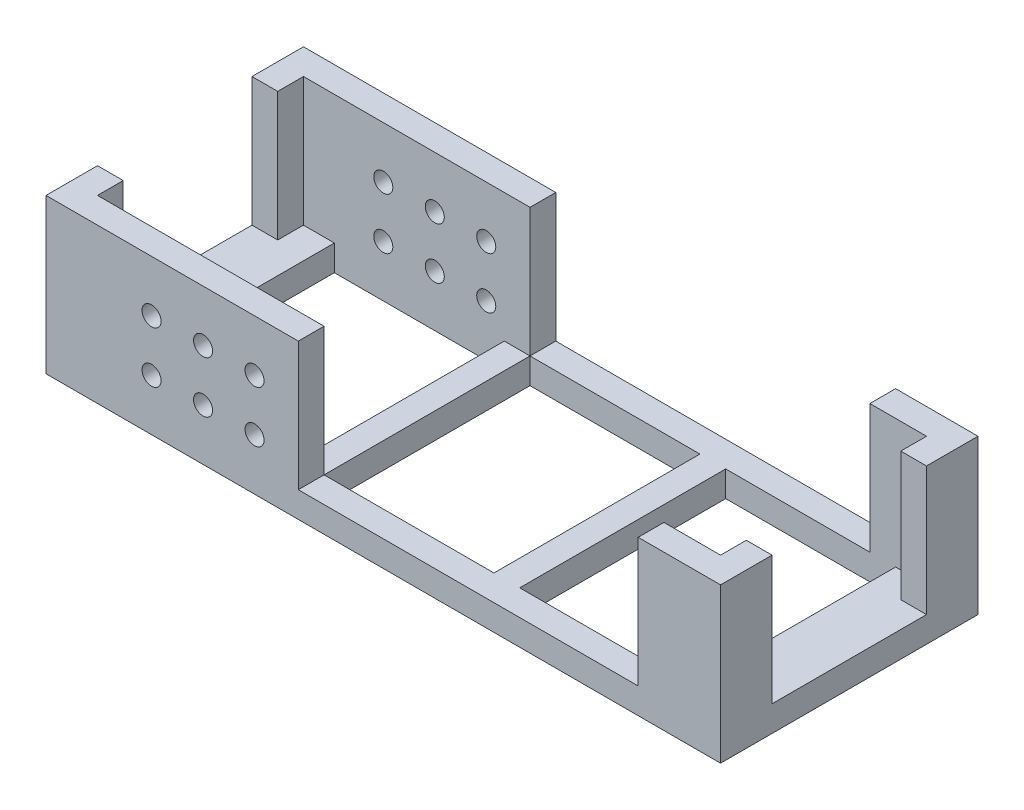
SolidWorks part; units mm, degrees
ref_plane "Front Plane" through (0, 0, 0) normal (0, 0, 1) x (1, 0, 0)
ref_plane "Top Plane" through (0, 0, 0) normal (0, 1, 0) x (1, 0, 0)
ref_plane "Right Plane" through (0, 0, 0) normal (1, 0, 0) x (0, 0, -1)
sketch "Sketch1" plane through (0, 0, 0) normal (0, 1, 0) x (1, 0, 0)
  line L1 (-65.5, -25) -> (65.5, -25)
  line L2 (-65.5, -25) -> (-65.5, 25)
  line L3 (-65.5, 25) -> (65.5, 25)
  line L4 (65.5, -25) -> (65.5, 25)
  line L5 (-65.5, -25) -> (65.5, 25) construction
  line L6 (-65.5, 25) -> (65.5, -25) construction
  point P0 (0, 0)
extrude "Boss-Extrude6" add sketch "Sketch1" along normal blind 5
sketch "Sketch11" plane through (0, 0, 0) normal (0, 1, 0) x (1, 0, 0)
  line L0 (54.5, -20) -> (21.5, -20)
  line L1 (16.5, -20) -> (-16.5, -20)
  line L2 (16.5, -20) -> (16.5, 20)
  line L3 (16.5, 20) -> (-16.5, 20)
  line L4 (-16.5, -20) -> (-16.5, 20)
  line L5 (16.5, -20) -> (-16.5, 20) construction
  line L6 (16.5, 20) -> (-16.5, -20) construction
  line L7 (54.5, -20) -> (54.5, 20)
  line L8 (54.5, 20) -> (21.5, 20)
  line L9 (21.5, -20) -> (21.5, 20)
  line L10 (54.5, -20) -> (21.5, 20) construction
  line L11 (54.5, 20) -> (21.5, -20) construction
  line L12 (-21.5, -20) -> (-54.5, -20)
  line L13 (-21.5, -20) -> (-21.5, 20)
  line L14 (-21.5, 20) -> (-54.5, 20)
  line L15 (-54.5, -20) -> (-54.5, 20)
  line L16 (-21.5, -20) -> (-54.5, 20) construction
  line L17 (-21.5, 20) -> (-54.5, -20) construction
  point P0 (0, 0)
  point P8 (38, 0)
  point P13 (-38, 0)
  dimension "D1" = 2
  dimension "D2" = 2
extrude "Cut-Extrude7" cut sketch "Sketch11" along normal blind 5
sketch "Sketch12" plane through (0, 0, 0) normal (0, 1, 0) x (1, 0, 0)
  line L0 (65.5, 25) -> (-65.5, 25) construction
  line L5 (-54.5, -20) -> (-60.5, -20) construction
  line L6 (-65.5, -25) -> (-59, -25)
  line L7 (-65.5, -25) -> (-65.5, 25)
  line L8 (-65.5, 25) -> (-59, 25)
  line L10 (-65.5, -25) -> (-16.5, -25)
  line L11 (-65.5, -25) -> (-65.5, -20)
  line L13 (-16.5, -25) -> (-16.5, -20)
  line L14 (-65.5, 25) -> (-16.5, 25)
  line L15 (-65.5, 25) -> (-65.5, 20)
  line L17 (-16.5, 25) -> (-16.5, 20)
  line L18 (-54.5, 20) -> (-60.5, 20) construction
  line L19 (-16.5, -20) -> (-60.5, -20)
  line L20 (-60.5, -20) -> (-60.5, 20)
  line L21 (-60.5, 20) -> (-16.5, 20)
  line L22 (54.5, -20) -> (60.5, -20) construction
  line L23 (65.5, -25) -> (65.5, 25)
  line L27 (60.5, 20) -> (60.5, -20)
  line L32 (54.5, -20) -> (49.5, -20) construction
  line L33 (65.5, -25) -> (49.5, -25)
  line L34 (-65.5, -25) -> (65.5, -25) construction
  line L35 (49.5, -25) -> (49.5, -20)
  line L36 (49.5, -20) -> (60.5, -20)
  line L37 (65.5, 25) -> (49.5, 25)
  line L38 (49.5, 25) -> (49.5, 20)
  line L39 (54.5, 20) -> (21.5, 20) construction
  line L40 (49.5, 20) -> (60.5, 20)
extrude "Boss-Extrude7" add sketch "Sketch12" along normal blind 30 contours L20 L21 L17 L14 L8 L7 L6 L10 L13 L19 | L38 L40 L27 L36 L35 L33 L23 L37
sketch "Sketch13" plane through (0, 0, 0) normal (1, 0, 0) x (0, 0, -1)
  line L0 (0, 0) -> (0, 17.5) construction
  line L2 (15, 5) -> (-15, 5)
  line L3 (15, 5) -> (15, 30)
  line L4 (15, 30) -> (-15, 30)
  line L5 (-15, 5) -> (-15, 30)
  line L6 (15, 5) -> (-15, 30) construction
  line L7 (15, 30) -> (-15, 5) construction
extrude "Cut-Extrude8" cut sketch "Sketch13" against normal through all both and the other way through all
sketch "Sketch15" plane through (0, 0, 0) normal (0, 0, 1) x (1, 0, 0)
  line L0 (0, 0) -> (-35, 0) construction
  line L1 (-35, 0) -> (-35, 10) construction
  circle A0 centre (-35, 10) radius 1.85
  circle A1 centre (-25, 10) radius 1.85
  circle A2 centre (-25, 20) radius 1.85
  circle A3 centre (-35, 20) radius 1.85
  circle A4 centre (-45, 10) radius 1.85
  circle A5 centre (-45, 20) radius 1.85
  circle A6 centre (-35, 20) radius 1.85
  dimension "D1" = 2
  dimension "D3" = 2
  dimension "D2" = 2
  dimension "D4" = 2
extrude "Cut-Extrude10" cut sketch "Sketch15" against normal through all both and the other way through all contours A0 | A3 | A2 | A1 | A5 | A4
